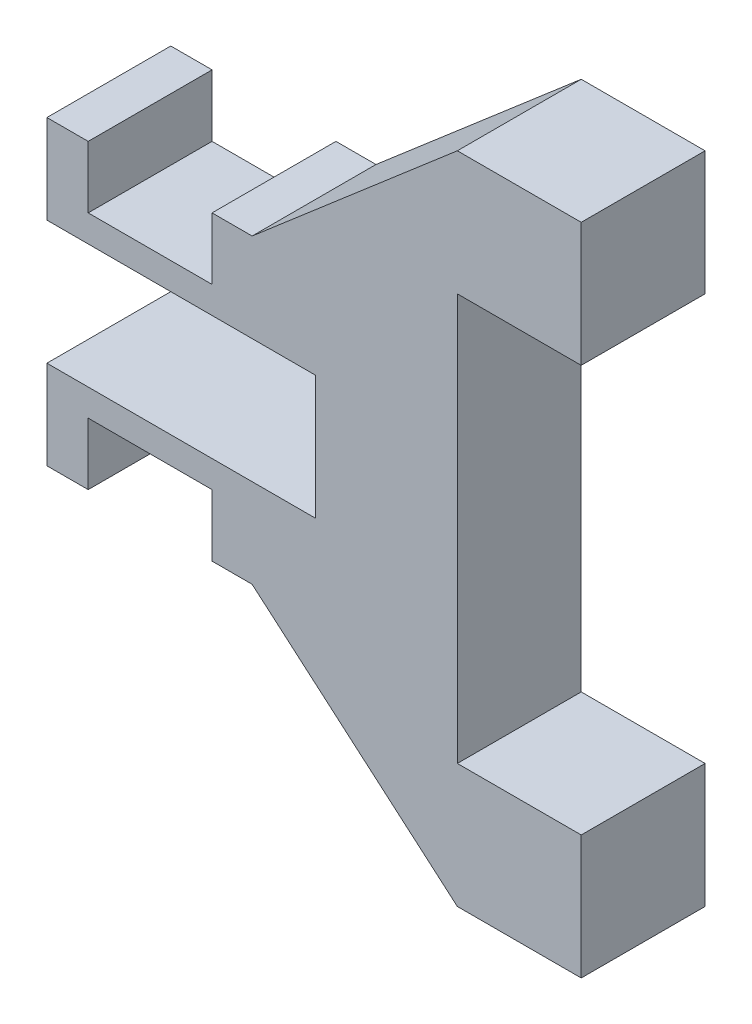
SolidWorks part; units mm, degrees
ref_plane "Front Plane" through (0, 0, 0) normal (0, 0, 1) x (1, 0, 0)
ref_plane "Top Plane" through (0, 0, 0) normal (0, 1, 0) x (1, 0, 0)
ref_plane "Right Plane" through (0, 0, 0) normal (1, 0, 0) x (0, 0, -1)
sketch "Sketch1" plane through (0, 0, 0) normal (0, 0, 1) x (1, 0, 0)
  line L0 (57.7184, 0) -> (57.7184, -1.524)
  line L1 (57.7184, 0) -> (57.7184, -1.524) construction
  line L2 (57.7184, -1.524) -> (54.4122, -1.524)
  line L3 (54.4122, -1.524) -> (54.4122, -2.6174)
  line L4 (54.4122, -2.6174) -> (56.937, -2.6174)
  line L5 (56.937, -2.6174) -> (59.4617, -4.7878)
  line L6 (59.4617, -4.7878) -> (60.9857, -4.7878)
  line L7 (60.9857, -4.7878) -> (60.9857, -3.2638)
  line L8 (60.9857, -3.2638) -> (59.4617, -3.2638)
  line L9 (59.4617, -3.2638) -> (59.4617, 1.7398)
  line L10 (59.4617, -1.524) -> (59.4617, 0) construction
  line L11 (59.4617, -0.762) -> (57.7184, -0.762) construction
  line L12 (60.9857, 1.7398) -> (59.4617, 1.7398)
  line L13 (60.9857, 3.2638) -> (60.9857, 1.7398)
  line L14 (59.4617, 3.2638) -> (60.9857, 3.2638)
  line L15 (56.937, 1.0934) -> (59.4617, 3.2638)
  line L16 (54.4122, 1.0934) -> (56.937, 1.0934)
  line L17 (54.4122, 0) -> (54.4122, 1.0934)
  line L18 (57.7184, 0) -> (54.4122, 0)
extrude "Boss-Extrude1" add sketch "Sketch1" along normal blind 1.524
ref_plane "Plane1" through (0, -0.762, 0) normal (0, 1, 0) x (1, 0, 0)
sketch "Sketch3" plane through (0, 1.0934, 0) normal (0, 1, 0) x (1, 0, 0)
  line L0 (56.937, 0) -> (54.4122, 0) construction
  line L1 (54.9202, 0) -> (56.4442, 0)
  line L2 (54.9202, 0) -> (54.9202, -1.524)
  line L3 (54.9202, -1.524) -> (56.4442, -1.524)
  line L4 (56.4442, 0) -> (56.4442, -1.524)
  line L5 (56.937, -1.524) -> (54.4122, -1.524) construction
  line L6 (54.4122, -1.524) -> (54.4122, 0) construction
  dimension "D1" = 1.524
  dimension "D2" = 0.508
extrude "Cut-Extrude1" cut sketch "Sketch3" against normal blind 0.762
mirror "Mirror1" about plane through (0, -0.762, 0) normal (0, 1, 0) of "Cut-Extrude1"
